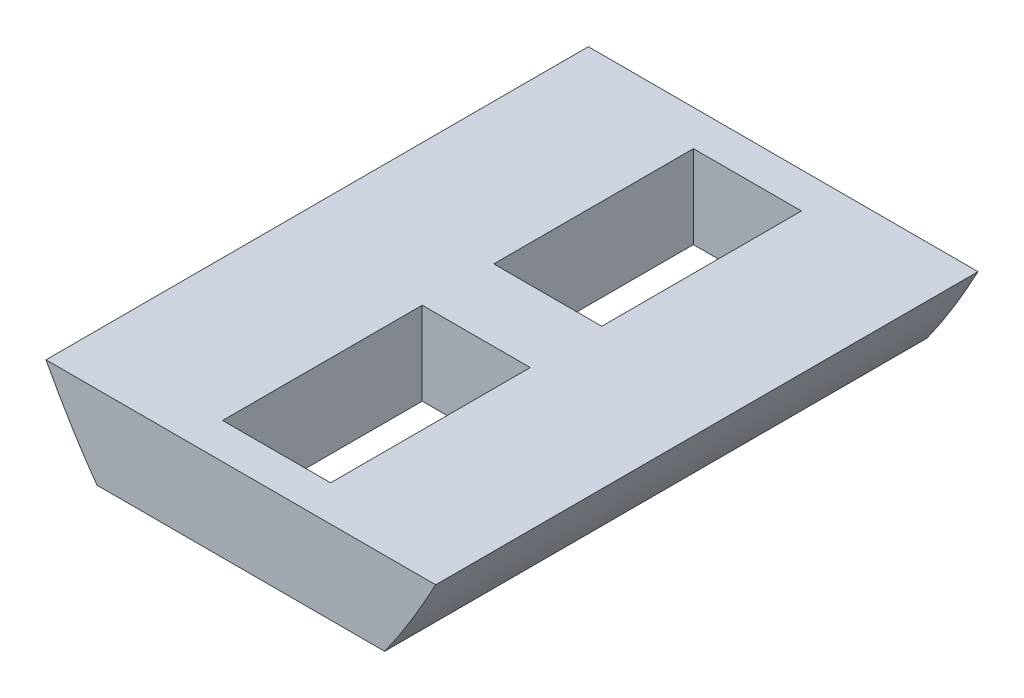
SolidWorks part; units mm, degrees
ref_plane "Front Plane" through (0, 0, 0) normal (0, 0, 1) x (1, 0, 0)
ref_plane "Top Plane" through (0, 0, 0) normal (0, 1, 0) x (1, 0, 0)
ref_plane "Right Plane" through (0, 0, 0) normal (1, 0, 0) x (0, 0, -1)
sketch "Sketch2" plane through (0, 0, 0) normal (0, 0, 1) x (1, 0, 0)
  line L0 (-127, 127) -> (127, 127)
  spline S0 degree 2 poles (-143.0272, 161.0769) (0, -161.0769) (143.0272, 161.0769) knots 0 0 0 1 1 1 construction
  spline S1 degree 2 poles (-127, 127) (0, -127) (127, 127) knots 0.056028 0.056028 0.056028 0.943972 0.943972 0.943972
extrude "Boss-Extrude2" add sketch "Sketch2" along normal blind 331.382
sketch "Sketch3" plane through (0, 127, 0) normal (0, 1, 0) x (1, 0, 0)
  line L0 (0, -309.5365) -> (0, 0) construction
  line L1 (-33, -21.8455) -> (33, -21.8455)
  line L2 (-33, -21.8455) -> (-33, -143.8455)
  line L3 (-33, -143.8455) -> (33, -143.8455)
  line L4 (33, -21.8455) -> (33, -143.8455)
  line L5 (-33, -187.5365) -> (33, -187.5365)
  line L6 (-33, -187.5365) -> (-33, -309.5365)
  line L7 (-33, -309.5365) -> (33, -309.5365)
  line L8 (33, -187.5365) -> (33, -309.5365)
  line L9 (-127, -165.691) -> (127, -165.691) construction
  line L10 (-127, -331.382) -> (-127, 0) construction
  line L11 (127, -331.382) -> (127, 0) construction
  line L12 (-33, -143.8455) -> (-33, -165.691) construction
  line L13 (33, -187.5365) -> (33, -165.691) construction
  line L14 (-33, -21.8455) -> (-33, 0) construction
  line L15 (127, 0) -> (-127, 0) construction
  dimension "D1" = 122
  dimension "D2" = 66
extrude "Cut-Extrude2" cut sketch "Sketch3" against normal through all
sketch "Sketch4" plane through (0, 0, 0) normal (0, 0, -1) x (-1, 0, 0)
  line L1 (-90, 60.8) -> (90, 60.8)
  line L2 (-90, 60.8) -> (-90, 0)
  line L3 (-90, 0) -> (90, 0)
  line L4 (90, 60.8) -> (90, 0)
  dimension "D1" = 60.8
  dimension "D2" = 180
extrude "Cut-Extrude3" cut sketch "Sketch4" against normal through all
sketch "Sketch5" plane through (0, 0, 331.382) normal (0, 0, 1) x (1, 0, 0)
  line L0 (0, 0) -> (0, 111.6) construction
  line L1 (-130, 131.6) -> (130, 131.6)
  line L2 (-130, 131.6) -> (-130, 111.6)
  line L3 (-130, 111.6) -> (130, 111.6)
  line L4 (130, 131.6) -> (130, 111.6)
  dimension "D1" = 111.6
  dimension "D2" = 260
  dimension "D3" = 20
extrude "Cut-Extrude4" cut sketch "Sketch5" against normal through all
